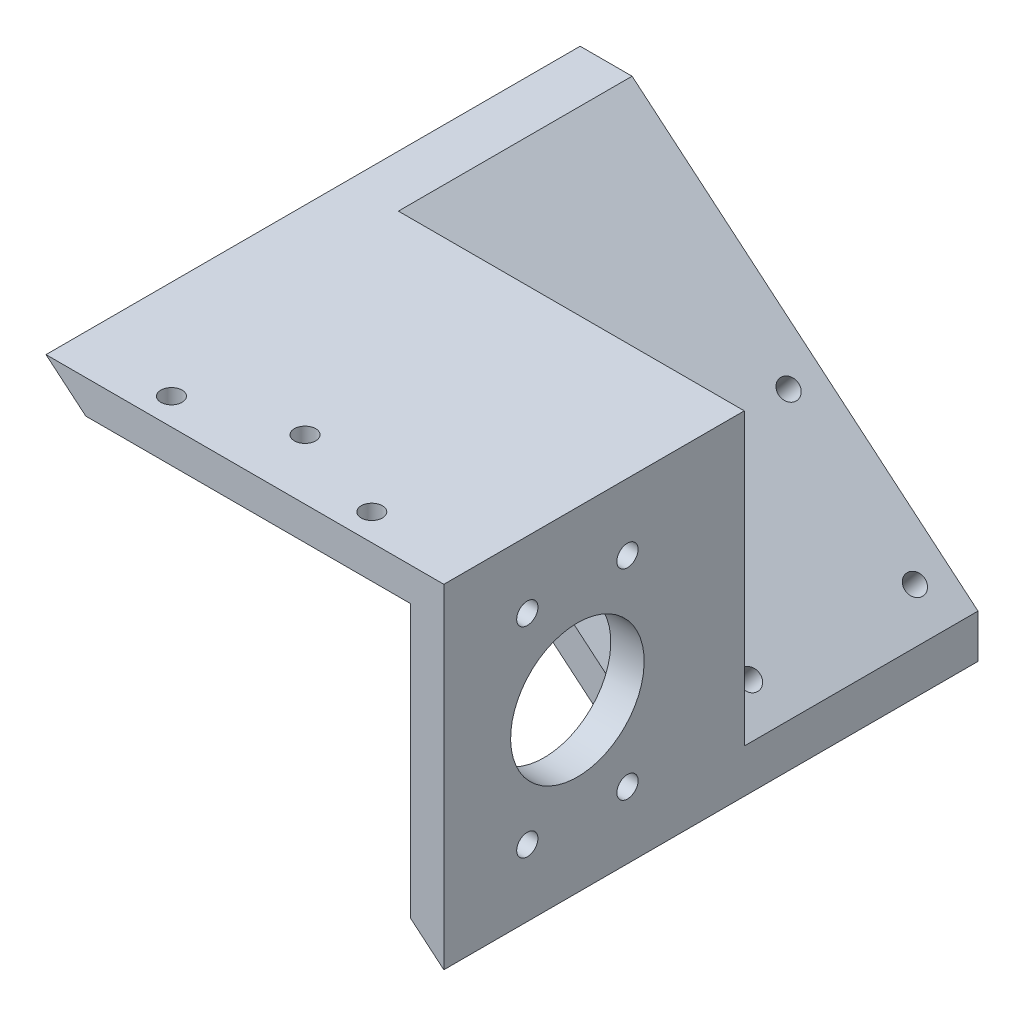
SolidWorks part; units mm, degrees
ref_plane "Front Plane" through (0, 0, 0) normal (0, 0, 1) x (1, 0, 0)
ref_plane "Top Plane" through (0, 0, 0) normal (0, 1, 0) x (1, 0, 0)
ref_plane "Right Plane" through (0, 0, 0) normal (1, 0, 0) x (0, 0, -1)
sketch "Sketch1" plane through (0, 0, 0) normal (0, 0, 1) x (1, 0, 0)
  line L0 (0, 0) -> (75.6764, 0)
  line L1 (75.6764, 0) -> (75.6764, -63.5)
  line L2 (75.6764, -63.5) -> (0, 0)
  line L3 (17.4465, -6.35) -> (69.3264, -6.35)
  line L4 (69.3264, -6.35) -> (69.3264, -49.8824)
  line L5 (69.3264, -49.8824) -> (17.4465, -6.35)
  dimension "D1" = 63.5
  dimension "D2" = 40
  dimension "D3" = 6.35
  dimension "D4" = 6.35
  dimension "D5" = 6.35
extrude "Boss-Extrude1" add sketch "Sketch1" along normal blind 101.6
sketch "Sketch3" plane through (0, 0, 0) normal (0, 1, 0) x (1, 0, 0)
  line L0 (75.6764, -101.6) -> (75.6764, 0) construction
  line L1 (0, -101.6) -> (69.3264, -101.6)
  line L2 (0, -101.6) -> (0, -57.15)
  line L3 (0, -57.15) -> (69.3264, -57.15)
  line L4 (69.3264, -101.6) -> (69.3264, -57.15)
  dimension "D1" = 6.35
  dimension "D2" = 44.45
extrude "Cut-Extrude2" cut sketch "Sketch3" against normal through all from offset 6.35 offset against normal yes
sketch "Sketch4" plane through (75.6764, 0, 0) normal (1, 0, 0) x (0, 0, -1)
  line L0 (-101.6, -63.5) -> (-101.6, 0) construction
  circle A0 centre (-76.2, -31.75) radius 12.7
  point P6 (-101.6, -31.75)
  dimension "D1" = 25.4
  dimension "D2" = 25.4
extrude "Cut-Extrude3" cut sketch "Sketch4" against normal up to next
sketch "Sketch5" plane through (75.6764, 0, 0) normal (1, 0, 0) x (0, 0, -1)
  line L0 (-101.6, -63.5) -> (-101.6, 0) construction
  line L1 (-85.725, -50.8) -> (-66.675, -50.8) construction
  line L2 (-85.725, -50.8) -> (-85.725, -12.7) construction
  line L3 (-85.725, -12.7) -> (-66.675, -12.7) construction
  line L4 (-66.675, -50.8) -> (-66.675, -12.7) construction
  line L5 (-76.2, -44.45) -> (-76.2, -19.05) construction
  circle A0 centre (-76.2, -31.75) radius 12.7 construction
  point P6 (-101.6, -31.75)
  point P7 (-76.2, -50.8)
  point P9 (-85.725, -31.75)
  dimension "D1" = 38.1
  dimension "D2" = 19.05
hole_wizard "#10-32 Tapped Hole1" positions "3DSketch1" profile "Sketch6" tap size "#10-32" standard "ANSI Inch" end condition up to next
sketch3d "3DSketch1"
  point P0 (75.6764, -50.8, 85.725)
  point P3 (75.6764, -50.8, 66.675)
  point P6 (75.6764, -12.7, 85.725)
  point P9 (75.6764, -12.7, 66.675)
sketch "Sketch6" plane through (75.6764, -50.8, 85.725) normal (0, 1, 0) x (0, 0, -1)
  line L0 (0, 0) -> (0, 6.35)
  line L1 (0, 6.35) -> (2.0193, 6.35)
  line L2 (2.0193, 6.35) -> (2.0193, 0)
  line L5 (2.0193, 0) -> (0, 0)
  line L11 (0, -6.35) -> (0, 107.95) construction
  dimension "Thru Tap Drill Dia." = 4.0386
  dimension "Thru Tap Drill Depth" = 6.35
cosmetic thread "Hole Thread1" parameters "D2"=4.826
cosmetic thread "Hole Thread2" parameters "D2"=4.826
cosmetic thread "Hole Thread3" parameters "D2"=4.826
cosmetic thread "Hole Thread4" parameters "D2"=4.826
sketch "Sketch7" plane through (0, 0, 0) normal (0, 1, 0) x (1, 0, 0)
  line L0 (56.8882, -96.52) -> (18.7882, -96.52) construction
  line L1 (18.7882, -96.52) -> (37.8382, -90.17) construction
  line L2 (37.8382, -90.17) -> (56.8882, -96.52) construction
  line L3 (75.6764, -101.6) -> (0, -101.6) construction
  point P5 (37.8382, -101.6)
  dimension "D1" = 38.1
  dimension "D2" = 5.08
  dimension "D3" = 6.35
hole_wizard "#10-32 Tapped Hole2" positions "Sketch9" profile "Sketch8" tap size "#10-32" standard "ANSI Inch" end condition up to next
sketch "Sketch9" plane through (0, 0, 0) normal (0, 1, 0) x (1, 0, 0)
  point P0 (56.8882, -96.52)
  point P3 (37.8382, -90.17)
  point P6 (18.7882, -96.52)
sketch "Sketch8" plane through (56.8882, 0, 96.52) normal (1, 0, 0) x (0, 0, 1)
  line L0 (0, 0) -> (0, 6.35)
  line L1 (0, 6.35) -> (2.0193, 6.35)
  line L2 (2.0193, 6.35) -> (2.0193, 0)
  line L5 (2.0193, 0) -> (0, 0)
  line L11 (0, -6.35) -> (0, 107.95) construction
  dimension "Thru Tap Drill Dia." = 4.0386
  dimension "Thru Tap Drill Depth" = 6.35
cosmetic thread "Hole Thread5" parameters "D2"=4.826
cosmetic thread "Hole Thread6" parameters "D2"=4.826
cosmetic thread "Hole Thread7" parameters "D2"=4.826
sketch "Sketch10" plane through (0, 0, 0) normal (0, 0, -1) x (-1, 0, 0)
  line L0 (-75.6764, -55.2107) -> (-9.8788, 0)
  line L1 (-75.6764, -63.5) -> (-75.6764, 0) construction
  line L2 (-75.6764, 0) -> (0, 0) construction
  line L3 (-56.8882, 0) -> (-18.7882, 0) construction
  line L4 (-9.8788, 0) -> (-75.6764, 0)
  line L5 (-75.6764, 0) -> (-75.6764, -55.2107)
  line L6 (-17.4465, -6.35) -> (-69.3264, -49.8824) construction
extrude "Cut-Extrude4" cut sketch "Sketch10" against normal blind 44.45
sketch "Sketch11" plane through (0, 0, 0) normal (-0.6428, -0.766, 0) x (0.766, -0.6428, 0)
  line L0 (98.7885, 101.6) -> (98.7885, 0) construction
  line L1 (54.7195, 37.719) -> (86.0885, 37.719) construction
  line L2 (54.7195, 37.719) -> (54.7195, 6.35) construction
  line L3 (54.7195, 6.35) -> (86.0885, 6.35) construction
  line L4 (86.0885, 37.719) -> (86.0885, 6.35) construction
  line L5 (0, 0) -> (98.7885, 0) construction
  circle A0 centre (54.7195, 37.719) radius 1.905
  circle A1 centre (86.0885, 37.719) radius 1.905
  circle A2 centre (54.7195, 6.35) radius 1.905
  circle A3 centre (86.0885, 6.35) radius 1.905
  dimension "D4" = 3.81
  dimension "D1" = 31.369
  dimension "D2" = 12.7
  dimension "D3" = 6.35
extrude "Cut-Extrude5" cut sketch "Sketch11" against normal up to next
